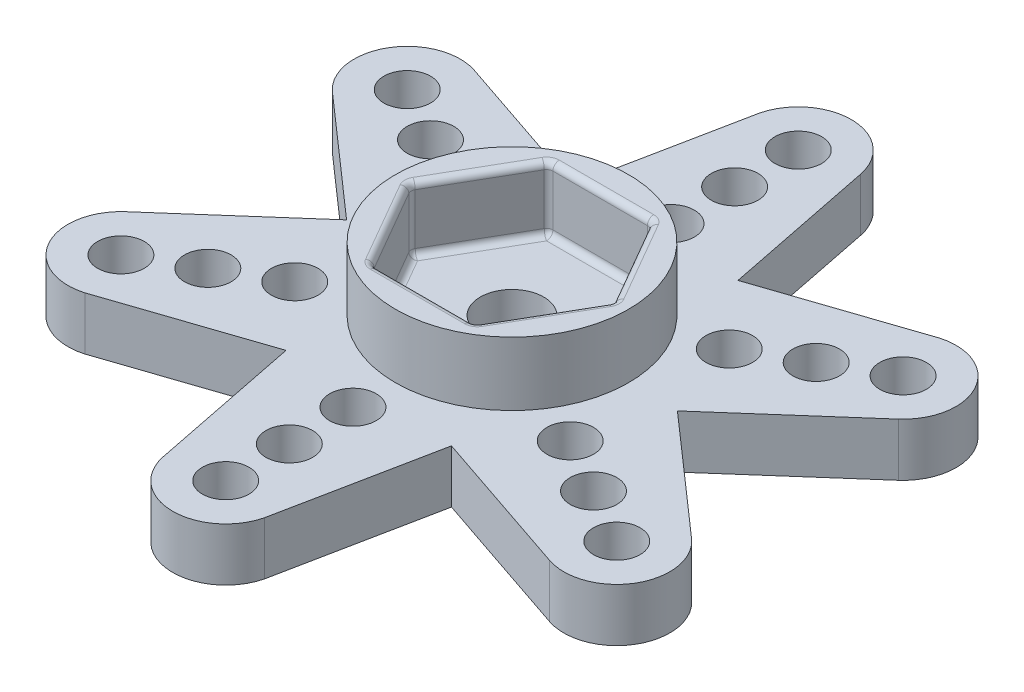
SolidWorks part; units mm, degrees
ref_plane "Alzado" through (0, 0, 0) normal (0, 0, 1) x (1, 0, 0)
ref_plane "Planta" through (0, 0, 0) normal (0, 1, 0) x (1, 0, 0)
ref_plane "Vista lateral" through (0, 0, 0) normal (1, 0, 0) x (0, 0, -1)
sketch "Croquis1" plane through (0, 0, 0) normal (0, 1, 0) x (1, 0, 0)
  line L0 (3.9, -6.755) -> (-3.9, -6.755) construction
  line L1 (0, 0) -> (0, -16) construction
  line L2 (-3.9, -6.755) -> (-10.9949, -9.151)
  line L3 (-13.342, -4.8725) -> (-7.8, 0)
  line L4 (-7.8, 0) -> (-13.4225, 4.9463)
  line L5 (-10.8907, 9.1183) -> (-3.9, 6.755)
  line L6 (-3.9, 6.755) -> (-2.4276, 14.0973)
  line L7 (2.4514, 13.9908) -> (3.9, 6.755)
  line L8 (3.9, 6.755) -> (10.9949, 9.151)
  line L9 (13.342, 4.8725) -> (7.8, 0)
  line L10 (3.9, -6.755) -> (2.4276, -14.0973)
  line L11 (7.8, 0) -> (13.4225, -4.9463)
  line L12 (-2.4514, -13.9908) -> (-3.9, -6.755)
  line L13 (10.8907, -9.1183) -> (3.9, -6.755)
  arc A0 (-13.342, -4.8725) -> (-10.9949, -9.151) centre (-11.6913, -6.75) ccw
  arc A1 (-10.8907, 9.1183) -> (-13.4225, 4.9463) centre (-11.6913, 6.75) ccw
  arc A2 (2.4514, 13.9908) -> (-2.4276, 14.0973) centre (0, 13.5) ccw
  arc A3 (13.342, 4.8725) -> (10.9949, 9.151) centre (11.6913, 6.75) ccw
  arc A4 (-2.4514, -13.9908) -> (2.4276, -14.0973) centre (0, -13.5) ccw
  arc A5 (10.8907, -9.1183) -> (13.4225, -4.9463) centre (11.6913, -6.75) ccw
  circle A6 centre (0, 0) radius 16 construction
  circle A8 centre (0, 0) radius 7.8 construction
  point P35 (0, 0)
  point P37 (0, 0)
  dimension "D1" = 32
  dimension "D5" = 5
  dimension "D2" = 15.6
extrude "Saliente-Extruir1" add sketch "Croquis1" along normal blind 2.5
sketch "Croquis2" plane through (0, 2.5, 0) normal (0, 1, 0) x (1, 0, 0)
  line L0 (0, 0) -> (0, -5.5) construction
  line L1 (2.4, -4.1569) -> (4.8, 0)
  line L2 (4.8, 0) -> (2.4, 4.1569)
  line L3 (2.4, 4.1569) -> (-2.4, 4.1569)
  line L4 (-2.4, 4.1569) -> (-4.8, 0)
  line L5 (-4.8, 0) -> (-2.4, -4.1569)
  line L6 (-2.4, -4.1569) -> (2.4, -4.1569)
  line L7 (0, 0) -> (2.4, -4.1569) construction
  circle A0 centre (0, 0) radius 5.5
  circle A1 centre (0, 0) radius 4.8 construction
  circle A2 centre (0, 0) radius 4.1569 construction
  dimension "D1" = 11
  dimension "D2" = 9.6
  dimension "D3" = 30
extrude "Saliente-Extruir2" add sketch "Croquis2" along normal blind 3
sketch "Croquis3" plane through (0, 0, 0) normal (0, -1, 0) x (1, 0, 0)
  circle A0 centre (0, 0) radius 1.5
  dimension "D1" = 3
extrude "Cortar-Extruir1" cut sketch "Croquis3" against normal up to next
sketch "Croquis4" plane through (0, 0, 0) normal (0, -1, 0) x (1, 0, 0)
  circle A0 centre (0, 0) radius 4.3
  dimension "D1" = 8.6
extrude "Cortar-Extruir2" cut sketch "Croquis4" against normal offset from surface (1 mm away) 1.5 up to face at (0, 2.5, 1.5)
sketch "Croquis5" plane through (0, 0, 0) normal (0, -1, 0) x (1, 0, 0)
  circle A0 centre (0, 0) radius 4.5
  circle A1 centre (0, 0) radius 4.3
  dimension "D1" = 9
  dimension "D2" = 8.6
extrude "Cortar-Extruir3" cut sketch "Croquis5" against normal blind 0.5
fillet "Redondeo1" radius 0.3 18 edges at (3.6, 5.5, -2.0785) (3.6, 5.5, 2.0785) (0, 5.5, 4.1569) (-3.6, 5.5, 2.0785) (-3.6, 5.5, -2.0785) (0, 5.5, -4.1569) (-2.4, 4, 4.1569) (-3.6, 2.5, 2.0785) (4.8, 4, 0) (2.4, 4, -4.1569) (3.6, 2.5, -2.0785) (0, 2.5, -4.1569) (-2.4, 4, -4.1569) (-3.6, 2.5, -2.0785) (-4.8, 4, 0) (0, 2.5, 4.1569) (2.4, 4, 4.1569) (3.6, 2.5, 2.0785)
sketch "Croquis6" plane through (0, 0, 0) normal (0, -1, 0) x (1, 0, 0)
  line L0 (0, 0) -> (0, -16.5) construction
  circle A0 centre (0, 0) radius 10.5 construction
  circle A1 centre (0, 0) radius 13.5 construction
  circle A3 centre (0, 0) radius 7.5 construction
  circle A5 centre (0, -13.5) radius 1.1
  circle A6 centre (0, -10.5) radius 1.1
  circle A7 centre (0, -7.5) radius 1.1
  dimension "D2" = 27
  dimension "D3" = 21
  dimension "D4" = 15
extrude "Cortar-Extruir4" cut sketch "Croquis6" against normal up to next (2.5 mm away)
pattern_circular "MatrizC1" count 6 over 360 about axis through (0, 0, 0) along (0, 1, 0) of "Cortar-Extruir4"
